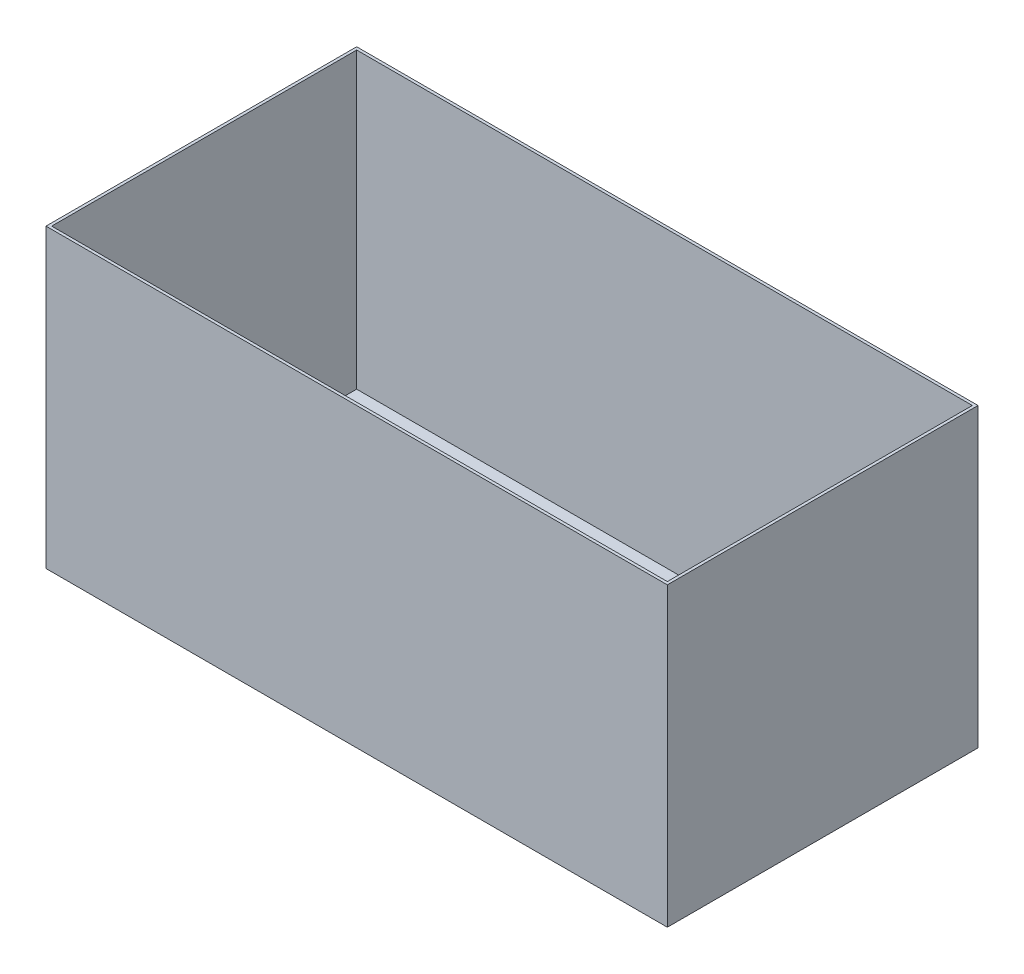
SolidWorks part; units mm, degrees
ref_plane "Front Plane" through (0, 0, 0) normal (0, 0, 1) x (1, 0, 0)
ref_plane "Top Plane" through (0, 0, 0) normal (0, 1, 0) x (1, 0, 0)
ref_plane "Right Plane" through (0, 0, 0) normal (1, 0, 0) x (0, 0, -1)
sketch "Sketch1" plane through (0, 0, 0) normal (0, 1, 0) x (1, 0, 0)
  line L1 (0, 0) -> (-2200, 0)
  line L2 (0, 0) -> (0, 1100)
  line L3 (0, 1100) -> (-2200, 1100)
  line L4 (-2200, 0) -> (-2200, 1100)
  dimension "D1" = 2200
  dimension "D2" = 1100
extrude "Extrude1" add sketch "Sketch1" along normal blind 1050
shell "Shell1" thickness 10
sketch "Sketch2" plane through (0, 0, 0) normal (0, -1, 0) x (1, 0, 0)
  line L0 (-2200, 0) -> (0, 0) construction
  line L1 (-100, -250) -> (-700, -250)
  line L2 (-100, -250) -> (-100, -850)
  line L3 (-100, -850) -> (-700, -850)
  line L4 (-700, -250) -> (-700, -850)
  line L5 (0, 0) -> (0, -1100) construction
  dimension "D1" = 600
  dimension "D2" = 600
  dimension "D3" = 250
  dimension "D4" = 100
extrude "Cut-Extrude1" cut sketch "Sketch2" against normal blind 400
